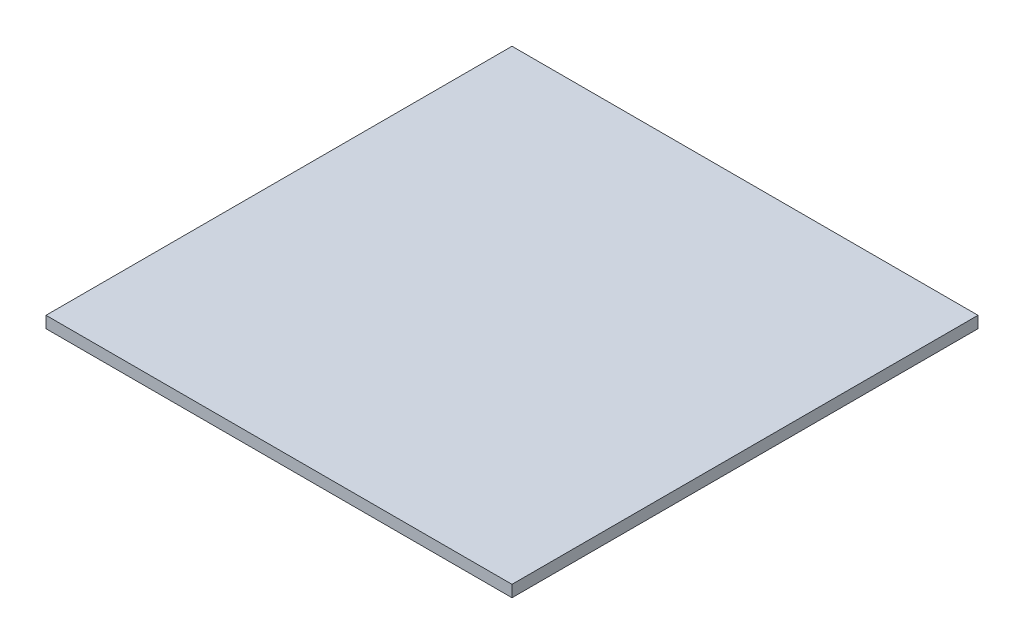
SolidWorks part; units mm, degrees
ref_plane "Alzado" through (0, 0, 0) normal (0, 0, 1) x (1, 0, 0)
ref_plane "Planta" through (0, 0, 0) normal (0, 1, 0) x (1, 0, 0)
ref_plane "Vista lateral" through (0, 0, 0) normal (1, 0, 0) x (0, 0, -1)
sketch "Croquis1" plane through (0, 0, 0) normal (0, 1, 0) x (1, 0, 0)
  line L1 (-15, 40) -> (15, 40)
  line L2 (-15, 40) -> (-15, -40)
  line L3 (-15, -40) -> (15, -40)
  line L4 (15, 40) -> (15, -40)
  line L5 (-15, 40) -> (15, -40) construction
  line L6 (-15, -40) -> (15, 40) construction
  point P0 (0, 0)
  dimension "D1" = 80
  dimension "D2" = 30
extrude "Saliente-Extruir1" add sketch "Croquis1" along normal blind 2
sketch "Croquis2" plane through (-15, 0, 0) normal (-1, 0, 0) x (0, 0, 1)
  line L4 (-40, 0) -> (40, 0)
  line L5 (40, 0) -> (40, 2)
  line L6 (40, 2) -> (-40, 2)
  line L7 (-40, 2) -> (-40, 0)
  line L8 (-40, 0) -> (40, 0)
  line L9 (40, 0) -> (40, 2)
  line L10 (40, 2) -> (-40, 2)
  line L11 (-40, 2) -> (-40, 0)
  dimension "D1" = 0
extrude "Saliente-Extruir2" add sketch "Croquis2" along normal blind 50
